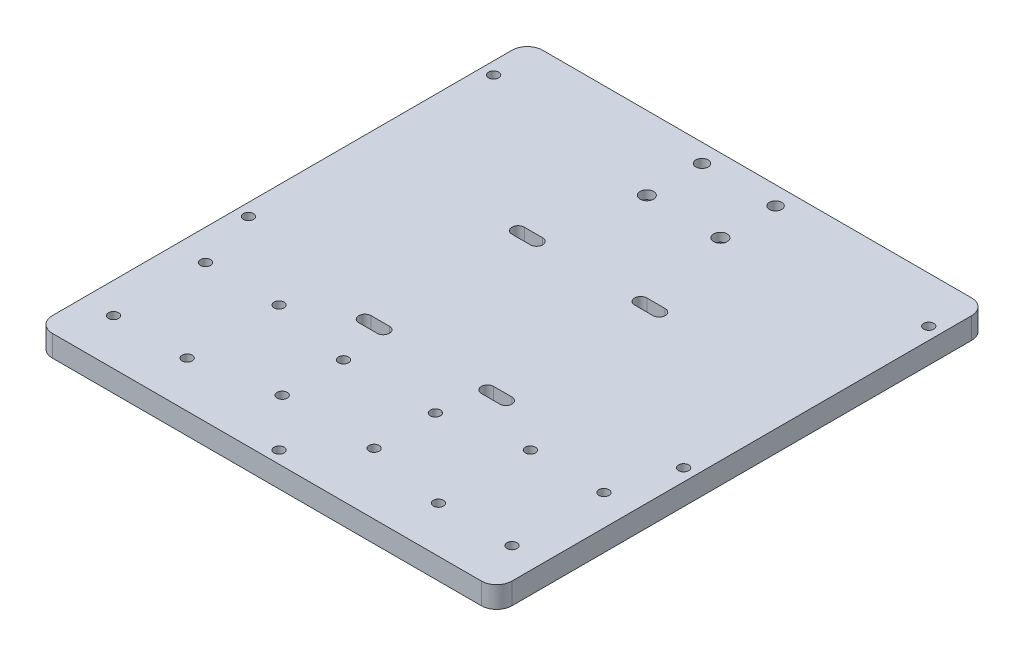
SolidWorks part; units mm, degrees
ref_plane "前视基准面" through (0, 0, 0) normal (0, 0, 1) x (1, 0, 0)
ref_plane "上视基准面" through (0, 0, 0) normal (0, 1, 0) x (1, 0, 0)
ref_plane "右视基准面" through (0, 0, 0) normal (1, 0, 0) x (0, 0, -1)
sketch "草图2" plane through (0, 0, 0) normal (0, 1, 0) x (1, 0, 0)
  line L1 (-75, 80) -> (75, 80)
  line L2 (-75, 80) -> (-75, -80)
  line L3 (-75, -80) -> (75, -80)
  line L4 (75, 80) -> (75, -80)
  line L5 (-75, 80) -> (75, -80) construction
  line L6 (-75, -80) -> (75, 80) construction
  point P0 (0, 0)
  dimension "D1" = 150
  dimension "D2" = 160
extrude "凸台-拉伸1" add sketch "草图2" along normal blind 7
fillet "圆角1" radius 5 4 edges at (-75, 3.5, 80) (75, 3.5, 80) (-75, 3.5, -80) (75, 3.5, -80)
sketch "草图3" plane through (0, 7, 0) normal (0, 1, 0) x (1, 0, 0)
  line L0 (0, 126.7071) -> (0, 0) construction
  line L1 (0, 0) -> (0, -132.3231) construction
  line L2 (-53, -50) -> (-53, -29.6783) construction
  line L3 (-65, -35) -> (-41, -35) construction
  line L4 (-65, -35) -> (-65, -65) construction
  line L5 (-65, -65) -> (-41, -65) construction
  line L6 (-41, -35) -> (-41, -65) construction
  line L7 (-65, -35) -> (-41, -65) construction
  line L8 (-65, -65) -> (-41, -35) construction
  line L9 (-53, -50) -> (-36.4908, -50) construction
  line L10 (-70, -80) -> (70, -80) construction
  line L11 (53, -50) -> (36.4908, -50) construction
  line L12 (65, -65) -> (41, -35) construction
  line L13 (65, -35) -> (41, -65) construction
  line L14 (41, -35) -> (41, -65) construction
  line L15 (65, -65) -> (41, -65) construction
  line L16 (65, -35) -> (65, -65) construction
  line L17 (65, -35) -> (41, -35) construction
  line L18 (-75, 75) -> (-75, -75) construction
  line L20 (-15, -40) -> (15, -40) construction
  line L21 (-15, -40) -> (-15, -60) construction
  line L22 (-15, -60) -> (15, -60) construction
  line L23 (15, -40) -> (15, -60) construction
  line L24 (-15, -40) -> (15, -60) construction
  line L25 (-15, -60) -> (15, -40) construction
  circle A0 centre (-65, -35) radius 1.65
  circle A1 centre (-41, -35) radius 1.65
  circle A2 centre (-41, -65) radius 1.65
  circle A3 centre (-65, -65) radius 1.65
  circle A4 centre (65, -65) radius 1.65
  circle A5 centre (41, -65) radius 1.65
  circle A6 centre (41, -35) radius 1.65
  circle A7 centre (65, -35) radius 1.65
  circle A8 centre (-15, -40) radius 1.65
  circle A9 centre (-15, -60) radius 1.65
  circle A10 centre (15, -60) radius 1.65
  circle A11 centre (15, -40) radius 1.65
  point P3 (-53, -50)
  point P31 (53, -50)
  point P34 (0, -50)
  dimension "D3" = 3.3
  dimension "D8" = 3.3
  dimension "D9" = 3.3
  dimension "D1" = 24
  dimension "D2" = 30
  dimension "D4" = 10
  dimension "D5" = 30
  dimension "D6" = 30
  dimension "D7" = 20
  dimension "D10" = 30
extrude "切除-拉伸1" cut sketch "草图3" against normal through all
sketch "草图4" plane through (0, 7, 0) normal (0, 1, 0) x (1, 0, 0)
  line L0 (-70, -80) -> (70, -80) construction
  line L1 (-20, 40) -> (20, 40)
  line L2 (-20, 40) -> (-20, -80)
  line L3 (-20, -80) -> (20, -80)
  line L4 (20, 40) -> (20, -80)
  line L5 (-20, 40) -> (20, -80) construction
  line L6 (-20, -80) -> (20, 40) construction
  point P0 (0, -20)
  dimension "D1" = 40
  dimension "D2" = 120
sketch "草图6" plane through (0, 7, 0) normal (0, 1, 0) x (1, 0, 0)
  line L0 (0, 0) -> (0, 24) construction
  line L1 (70, 80) -> (-70, 80) construction
  line L2 (-12, 74) -> (12, 74) construction
  line L3 (-12, 74) -> (-12, 56) construction
  line L4 (-12, 56) -> (12, 56) construction
  line L5 (12, 74) -> (12, 56) construction
  line L6 (-12, 74) -> (12, 56) construction
  line L7 (-12, 56) -> (12, 74) construction
  circle A0 centre (12, 74) radius 2.02
  circle A1 centre (12, 56) radius 2.2
  circle A2 centre (-12, 56) radius 2.2
  circle A3 centre (-12, 74) radius 2.02
  point P3 (0, 65)
  dimension "D4" = 4.04
  dimension "D5" = 4.4
  dimension "D1" = 24
  dimension "D2" = 18
  dimension "D3" = 6
extrude "切除-拉伸2" cut sketch "草图6" against normal through all
sketch "草图8" plane through (0, 7, 0) normal (0, 1, 0) x (1, 0, 0)
  line L0 (0, 0) -> (0, -108.8205) construction
  circle A0 centre (-15, -40) radius 3.15
  circle A1 centre (-15, -60) radius 3.15
  circle A2 centre (15, -60) radius 3.15
  circle A3 centre (15, -40) radius 3.15
  dimension "D1" = 6.3
  dimension "D2" = 6.3
sketch "草图9" plane through (0, 0, 0) normal (0, -1, 0) x (1, 0, 0)
  line L0 (0, 0) -> (0, 99.7437) construction
  line L1 (-39.3257, 67.9) -> (-37.6514, 65)
  line L2 (61.6514, 35) -> (63.3257, 32.1)
  line L3 (63.3257, 32.1) -> (66.6743, 32.1)
  line L4 (66.6743, 32.1) -> (68.3486, 35)
  line L5 (68.3486, 35) -> (66.6743, 37.9)
  line L6 (66.6743, 37.9) -> (63.3257, 37.9)
  line L7 (63.3257, 37.9) -> (61.6514, 35)
  line L8 (37.6514, 35) -> (39.3257, 32.1)
  line L9 (39.3257, 32.1) -> (42.6743, 32.1)
  line L10 (42.6743, 32.1) -> (44.3486, 35)
  line L11 (44.3486, 35) -> (42.6743, 37.9)
  line L12 (42.6743, 37.9) -> (39.3257, 37.9)
  line L13 (39.3257, 37.9) -> (37.6514, 35)
  line L14 (61.6514, 65) -> (63.3257, 62.1)
  line L15 (63.3257, 62.1) -> (66.6743, 62.1)
  line L16 (66.6743, 62.1) -> (68.3486, 65)
  line L17 (68.3486, 65) -> (66.6743, 67.9)
  line L18 (66.6743, 67.9) -> (63.3257, 67.9)
  line L19 (63.3257, 67.9) -> (61.6514, 65)
  line L20 (37.6514, 65) -> (39.3257, 62.1)
  line L21 (39.3257, 62.1) -> (42.6743, 62.1)
  line L22 (42.6743, 62.1) -> (44.3486, 65)
  line L23 (44.3486, 65) -> (42.6743, 67.9)
  line L24 (42.6743, 67.9) -> (39.3257, 67.9)
  line L25 (39.3257, 67.9) -> (37.6514, 65)
  line L26 (-42.6743, 67.9) -> (-39.3257, 67.9)
  line L27 (-44.3486, 65) -> (-42.6743, 67.9)
  line L28 (-42.6743, 62.1) -> (-44.3486, 65)
  line L29 (-39.3257, 62.1) -> (-42.6743, 62.1)
  line L30 (-37.6514, 65) -> (-39.3257, 62.1)
  line L31 (-63.3257, 67.9) -> (-61.6514, 65)
  line L32 (-66.6743, 67.9) -> (-63.3257, 67.9)
  line L33 (-68.3486, 65) -> (-66.6743, 67.9)
  line L34 (-66.6743, 62.1) -> (-68.3486, 65)
  line L35 (-63.3257, 62.1) -> (-66.6743, 62.1)
  line L36 (-61.6514, 65) -> (-63.3257, 62.1)
  line L37 (-39.3257, 37.9) -> (-37.6514, 35)
  line L38 (-42.6743, 37.9) -> (-39.3257, 37.9)
  line L39 (-44.3486, 35) -> (-42.6743, 37.9)
  line L40 (-42.6743, 32.1) -> (-44.3486, 35)
  line L41 (-39.3257, 32.1) -> (-42.6743, 32.1)
  line L42 (-37.6514, 35) -> (-39.3257, 32.1)
  line L43 (-63.3257, 37.9) -> (-61.6514, 35)
  line L44 (-66.6743, 37.9) -> (-63.3257, 37.9)
  line L45 (-68.3486, 35) -> (-66.6743, 37.9)
  line L46 (-66.6743, 32.1) -> (-68.3486, 35)
  line L47 (-63.3257, 32.1) -> (-66.6743, 32.1)
  line L48 (-61.6514, 35) -> (-63.3257, 32.1)
  circle A0 centre (-15, 60) radius 3.15 construction
  circle A1 centre (-15, 40) radius 3.15 construction
  circle A2 centre (15, 60) radius 3.15 construction
  circle A3 centre (15, 40) radius 3.15 construction
  circle A4 centre (-15, 60) radius 3.15
  circle A5 centre (-15, 40) radius 3.15
  circle A6 centre (15, 60) radius 3.15
  circle A7 centre (15, 40) radius 3.15
  circle A8 centre (65, 35) radius 2.9 construction
  circle A9 centre (41, 35) radius 2.9 construction
  circle A10 centre (65, 65) radius 2.9 construction
  circle A11 centre (41, 65) radius 2.9 construction
  circle A12 centre (-41, 65) radius 2.9 construction
  circle A13 centre (-65, 65) radius 2.9 construction
  circle A14 centre (-41, 35) radius 2.9 construction
  circle A15 centre (-65, 35) radius 2.9 construction
  dimension "D1" = 5.8
  dimension "D2" = 5.8
  dimension "D3" = 5.8
  dimension "D4" = 5.8
extrude "切除-拉伸4" cut sketch "草图9" against normal blind 3.5
sketch "草图10" plane through (0, 0, 0) normal (0, -1, 0) x (1, 0, 0)
  line L0 (0, 0) -> (0, -118.0769) construction
  circle A0 centre (12, -74) radius 3.75
  circle A1 centre (12, -56) radius 3.75
  circle A2 centre (-12, -56) radius 3.75
  circle A3 centre (-12, -74) radius 3.75
  dimension "D1" = 7.5
  dimension "D2" = 7.5
extrude "切除-拉伸5" cut sketch "草图10" against normal blind 4.2
sketch "草图11" plane through (0, 7, 0) normal (0, 1, 0) x (1, 0, 0)
  line L0 (0, 0) -> (0, 194.7593) construction
  line L1 (17, 25) -> (23, 25) construction
  line L4 (17, 27) -> (23, 27)
  line L5 (17, 23) -> (23, 23)
  line L6 (0, 0) -> (-45.0628, 0) construction
  line L7 (-17, 25) -> (-23, 25) construction
  line L8 (-17, 27) -> (-23, 27)
  line L9 (-17, 23) -> (-23, 23)
  line L10 (17, -25) -> (23, -25) construction
  line L11 (17, -27) -> (23, -27)
  line L12 (17, -23) -> (23, -23)
  line L13 (-17, -25) -> (-23, -25) construction
  line L14 (-17, -27) -> (-23, -27)
  line L15 (-17, -23) -> (-23, -23)
  arc A2 (17, 27) -> (17, 23) centre (17, 25) ccw
  arc A3 (23, 23) -> (23, 27) centre (23, 25) ccw
  arc A4 (-17, 27) -> (-17, 23) centre (-17, 25) cw
  arc A5 (-23, 23) -> (-23, 27) centre (-23, 25) cw
  arc A6 (17, -27) -> (17, -23) centre (17, -25) cw
  arc A7 (23, -23) -> (23, -27) centre (23, -25) cw
  arc A8 (-17, -27) -> (-17, -23) centre (-17, -25) ccw
  arc A9 (-23, -23) -> (-23, -27) centre (-23, -25) ccw
  point P5 (20, 25)
  point P14 (-20, 25)
  point P21 (20, -25)
  point P28 (-20, -25)
  dimension "D2" = 2
  dimension "D1" = 6
  dimension "D3" = 20
  dimension "D4" = 25
extrude "切除-拉伸6" cut sketch "草图11" against normal through all
sketch "草图12" plane through (0, 0, 0) normal (0, -1, 0) x (1, 0, 0)
  line L0 (0, 0) -> (0, -131.8819) construction
  line L9 (70, -80) -> (-70, -80) construction
  line L10 (-71, -65) -> (71, -65) construction
  line L11 (-71, -65) -> (-71, 15) construction
  line L12 (-71, 15) -> (71, 15) construction
  line L13 (71, -65) -> (71, 15) construction
  line L14 (-71, -65) -> (71, 15) construction
  line L15 (-71, 15) -> (71, -65) construction
  circle A1 centre (-71, -65) radius 1.65
  circle A2 centre (-71, 15) radius 1.65
  circle A3 centre (71, 15) radius 1.65
  circle A4 centre (71, -65) radius 1.65
  point P2 (0, -25)
  dimension "D3" = 3.3
  dimension "D4" = 3.3
  dimension "D1" = 15
  dimension "D2" = 80
  dimension "D5" = 142
extrude "切除-拉伸7" cut sketch "草图12" against normal blind 50
sketch "草图14" plane through (0, 0, 0) normal (0, -1, 0) x (1, 0, 0)
  circle A0 centre (-71, -65) radius 3
  circle A1 centre (-71, 15) radius 3
  circle A2 centre (71, -65) radius 3
  circle A3 centre (71, 15) radius 3
  dimension "D1" = 6
  dimension "D2" = 6
  dimension "D3" = 6
  dimension "D4" = 6
extrude "切除-拉伸9" cut sketch "草图14" against normal blind 3.3
sketch "草图15" plane through (0, 0, 0) normal (0, -1, 0) x (1, 0, 0)
  line L0 (-70, 80) -> (70, 80) construction
  circle A0 centre (0, 76) radius 1.65
  dimension "D2" = 3.3
  dimension "D1" = 4
extrude "切除-拉伸10" cut sketch "草图15" against normal through all
sketch "草图16" plane through (0, 0, 0) normal (0, -1, 0) x (1, 0, 0)
  circle A0 centre (0, 76) radius 3
  dimension "D1" = 6
extrude "切除-拉伸11" cut sketch "草图16" against normal blind 3.3
